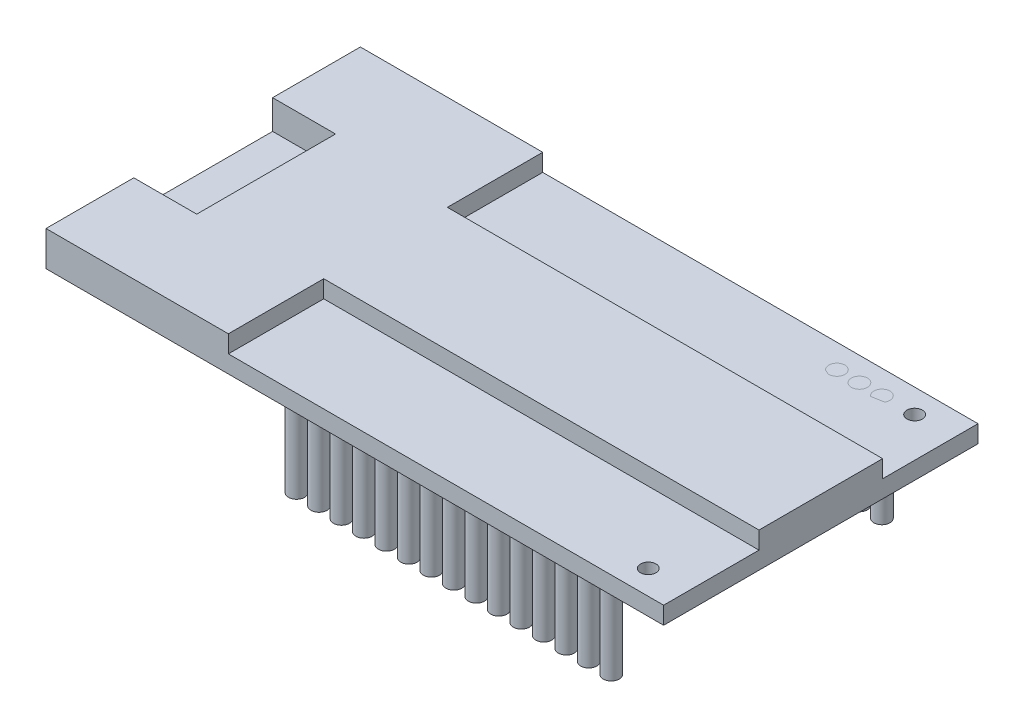
SolidWorks part; units mm, degrees
ref_plane "Front Plane" through (0, 0, 0) normal (0, 0, 1) x (1, 0, 0)
ref_plane "Top Plane" through (0, 0, 0) normal (0, 1, 0) x (1, 0, 0)
ref_plane "Right Plane" through (0, 0, 0) normal (1, 0, 0) x (0, 0, -1)
sketch "Sketch1" plane through (0, 0, 0) normal (0, 1, 0) x (1, 0, 0)
  line L1 (-27.475, -13.985) -> (27.475, -13.985)
  line L2 (-27.475, -13.985) -> (-27.475, 13.985)
  line L3 (-27.475, 13.985) -> (27.475, 13.985)
  line L4 (27.475, -13.985) -> (27.475, 13.985)
  line L5 (-27.475, -13.985) -> (27.475, 13.985) construction
  line L6 (-27.475, 13.985) -> (27.475, -13.985) construction
  point P0 (0, 0)
extrude "Boss-Extrude1" add sketch "Sketch1" along normal blind 3.1
sketch "Sketch2" plane through (0, 3.1, 0) normal (0, 1, 0) x (1, 0, 0)
  circle A20 centre (23.9546, 11.8718) radius 0.6903
  circle A21 centre (23.9546, -11.8297) radius 0.6882
extrude "Cut-Extrude1" cut sketch "Sketch2" against normal blind 3.1
sketch "Sketch3" plane through (0, 3.1, 0) normal (0, 1, 0) x (1, 0, 0)
  line L1 (27.475, 13.985) -> (-11.25, 13.985)
  line L2 (27.475, 13.985) -> (27.475, 5.5)
  line L3 (27.475, 5.5) -> (-11.25, 5.5)
  line L4 (-11.25, 13.985) -> (-11.25, 5.5)
  line L5 (27.475, -13.985) -> (-11.25, -13.985)
  line L6 (27.475, -13.985) -> (27.475, -5.5)
  line L7 (27.475, -5.5) -> (-11.25, -5.5)
  line L8 (-11.25, -13.985) -> (-11.25, -5.5)
extrude "Cut-Extrude2" cut sketch "Sketch3" against normal blind 1.55
sketch "Sketch4" plane through (0, 1.55, 0) normal (0, 1, 0) x (1, 0, 0)
  circle A0 centre (21.0422, 11.8658) radius 0.7174
  circle A1 centre (21.0422, -12.211) radius 0.7174
  circle A2 centre (19.0422, -12.211) radius 0.7174
  circle A3 centre (17.0422, -12.211) radius 0.7174
  circle A4 centre (15.0422, -12.211) radius 0.7174
  circle A5 centre (13.0422, -12.211) radius 0.7174
  circle A6 centre (11.0422, -12.211) radius 0.7174
  circle A7 centre (9.0422, -12.211) radius 0.7174
  circle A8 centre (7.0422, -12.211) radius 0.7174
  circle A9 centre (5.0422, -12.211) radius 0.7174
  circle A10 centre (3.0422, -12.211) radius 0.7174
  circle A11 centre (1.0422, -12.211) radius 0.7174
  circle A12 centre (-0.9578, -12.211) radius 0.7174
  circle A13 centre (-2.9578, -12.211) radius 0.7174
  circle A14 centre (-4.9578, -12.211) radius 0.7174
  circle A15 centre (-6.9578, -12.211) radius 0.7174
  circle A16 centre (19.0422, 11.8658) radius 0.7174
  circle A17 centre (17.0422, 11.8658) radius 0.7174
  circle A18 centre (15.0422, 11.8658) radius 0.7174
  circle A19 centre (13.0422, 11.8658) radius 0.7174
  circle A20 centre (11.0422, 11.8658) radius 0.7174
  circle A21 centre (9.0422, 11.8658) radius 0.7174
  circle A22 centre (7.0422, 11.8658) radius 0.7174
  circle A23 centre (5.0422, 11.8658) radius 0.7174
  circle A24 centre (3.0422, 11.8658) radius 0.7174
  circle A25 centre (1.0422, 11.8658) radius 0.7174
  circle A26 centre (-0.9578, 11.8658) radius 0.7174
  circle A27 centre (-2.9578, 11.8658) radius 0.7174
  circle A28 centre (-4.9578, 11.8658) radius 0.7174
  circle A29 centre (-6.9578, 11.8658) radius 0.7174
extrude "Boss-Extrude2" add sketch "Sketch4" against normal blind 9.44 separate body
sketch "Sketch5" plane through (0, 3.1, 0) normal (0, 1, 0) x (1, 0, 0)
  line L0 (-27.475, 13.985) -> (-27.475, -13.985) construction
  line L1 (-27.475, 4.175) -> (-21.875, 4.175)
  line L2 (-27.475, 4.175) -> (-27.475, -4.175)
  line L3 (-27.475, -4.175) -> (-21.875, -4.175)
  line L4 (-21.875, 4.175) -> (-21.875, -4.175)
  line L5 (-27.475, -13.985) -> (-11.25, -13.985) construction
  line L8 (-11.25, 13.985) -> (-27.475, 13.985) construction
  dimension "D1" = 9.81
  dimension "D2" = 9.81
extrude "Cut-Extrude3" cut sketch "Sketch5" against normal blind 2.6
chamfer "Chamfer1" distance 2 angle 45 2 edges at (-24.675, 3.1, -4.175) (-24.675, 3.1, 4.175)
sketch "Sketch6" plane through (-27.475, 0, 0) normal (-1, 0, 0) x (0, 0, 1)
  line L1 (-6.175, 3.1) -> (-4.175, 3.1)
  line L2 (-6.175, 3.1) -> (-6.175, 0.5)
  line L3 (-6.175, 0.5) -> (-4.175, 0.5)
  line L4 (-4.175, 3.1) -> (-4.175, 0.5)
  line L5 (6.175, 3.1) -> (4.175, 3.1)
  line L6 (6.175, 3.1) -> (6.175, 0.5)
  line L7 (6.175, 0.5) -> (4.175, 0.5)
  line L8 (4.175, 3.1) -> (4.175, 0.5)
  point P12 (0, 0)
  point P13 (0, 0)
  point P14 (0, 0)
extrude "Cut-Extrude5" cut sketch "Sketch6" against normal up to vertex (5.6 mm away)
